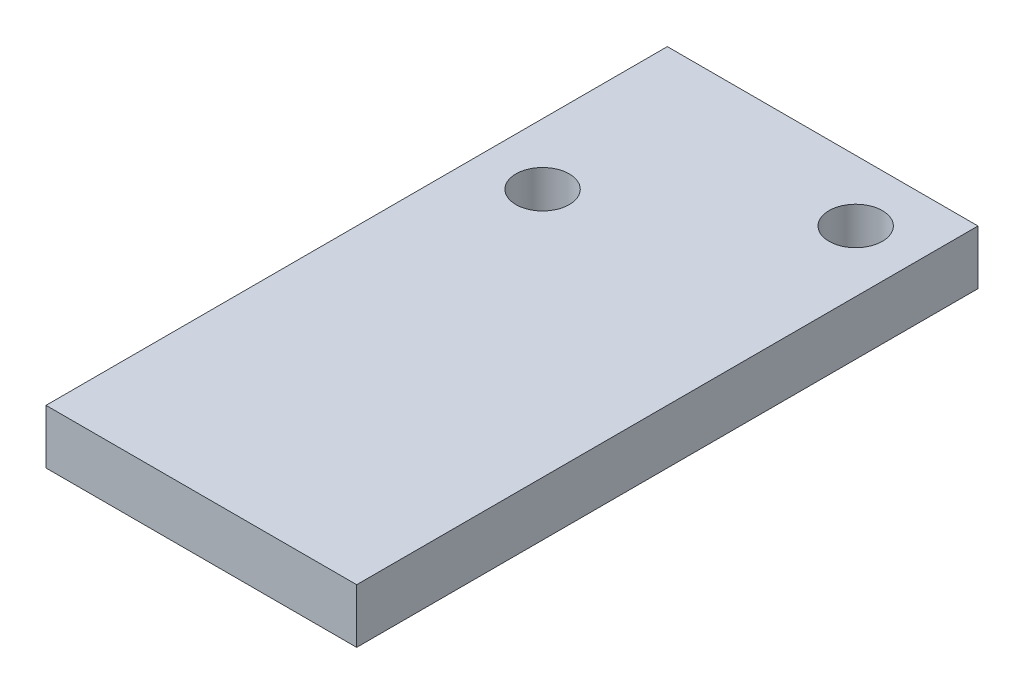
SolidWorks part; units mm, degrees
ref_plane "Front Plane" through (0, 0, 0) normal (0, 0, 1) x (1, 0, 0)
ref_plane "Top Plane" through (0, 0, 0) normal (0, 1, 0) x (1, 0, 0)
ref_plane "Right Plane" through (0, 0, 0) normal (1, 0, 0) x (0, 0, -1)
sketch "Sketch1" plane through (0, 0, 0) normal (0, 1, 0) x (1, 0, 0)
  line L1 (0, 0) -> (12.7, 0)
  line L2 (0, 0) -> (0, 25.4)
  line L3 (0, 25.4) -> (12.7, 25.4)
  line L4 (12.7, 0) -> (12.7, 25.4)
  circle A0 centre (2.5, 17.8) radius 1.09
  circle A1 centre (10.2, 22.9) radius 1.09
  dimension "D3" = 2.18
  dimension "D4" = 2.18
  dimension "D1" = 25.4
  dimension "D2" = 12.7
  dimension "D5" = 7.6
  dimension "D6" = 2.5
  dimension "D7" = 2.5
  dimension "D8" = 2.5
extrude "Boss-Extrude1" add sketch "Sketch1" along normal blind 2.22
